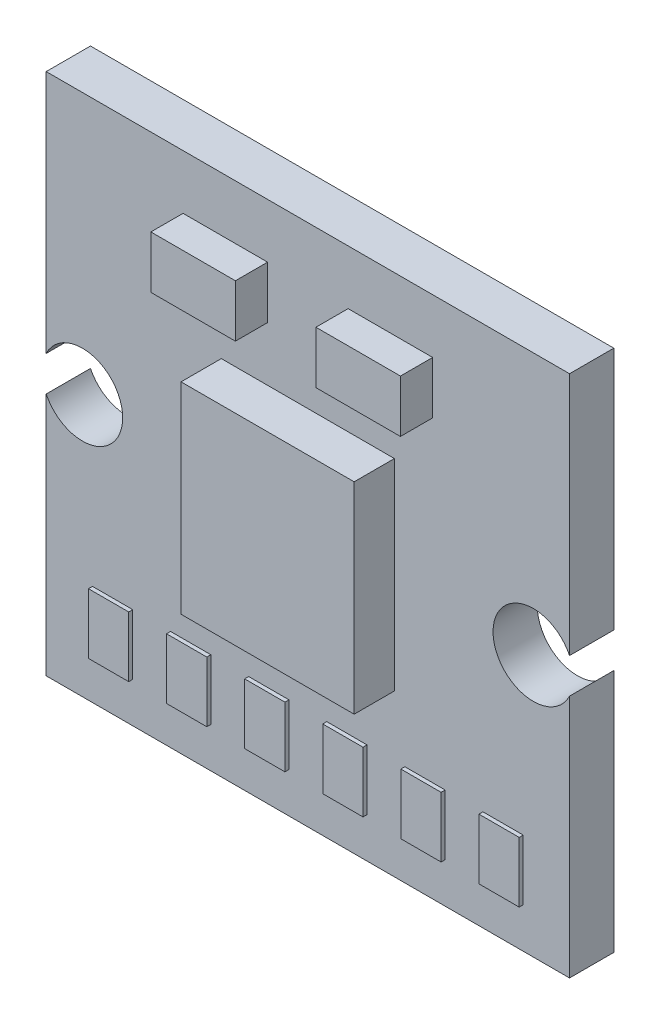
SolidWorks part; units mm, degrees
ref_plane "정면" through (0, 0, 0) normal (0, 0, 1) x (1, 0, 0)
ref_plane "윗면" through (0, 0, 0) normal (0, 1, 0) x (1, 0, 0)
ref_plane "우측면" through (0, 0, 0) normal (1, 0, 0) x (0, 0, -1)
sketch "스케치1" plane through (0, 0, 0) normal (0, 0, 1) x (1, 0, 0)
  line L1 (6.5, 6.5) -> (-6.5, 6.5)
  line L2 (6.5, 6.5) -> (6.5, -6.5)
  line L3 (6.5, -6.5) -> (-6.5, -6.5)
  line L4 (-6.5, 6.5) -> (-6.5, -6.5)
  point P0 (0, 6.5)
  point P1 (6.5, 0)
  dimension "D1" = 13
  dimension "D2" = 13
extrude "보스-돌출1" add sketch "스케치1" along normal blind 1.1
sketch "스케치2" plane through (0, 0, 1.1) normal (0, 0, 1) x (1, 0, 0)
  line L1 (-2.15, -2.5) -> (2.15, -2.5)
  line L2 (-2.15, -2.5) -> (-2.15, 2.5)
  line L3 (-2.15, 2.5) -> (2.15, 2.5)
  line L4 (2.15, -2.5) -> (2.15, 2.5)
  line L5 (-2.15, -2.5) -> (2.15, 2.5) construction
  line L6 (-2.15, 2.5) -> (2.15, -2.5) construction
  point P0 (0, 0)
  point P6 (0, 0)
  dimension "D1" = 5
  dimension "D2" = 4.3
extrude "보스-돌출2" add sketch "스케치2" along normal offset from surface (1 mm away) 2.1 up to face at (0, 0, 0)
sketch "스케치3" plane through (0, 0, 1.1) normal (0, 0, 1) x (1, 0, 0)
  line L0 (6.5, -6.5) -> (6.5, 6.5) construction
  line L1 (-3.1, 5.15) -> (-1, 5.15)
  line L2 (-3.1, 5.15) -> (-3.1, 3.85)
  line L3 (-3.1, 3.85) -> (-1, 3.85)
  line L4 (-1, 5.15) -> (-1, 3.85)
  line L5 (1, 5.15) -> (3.1, 5.15)
  line L6 (1, 5.15) -> (1, 3.85)
  line L7 (1, 3.85) -> (3.1, 3.85)
  line L8 (3.1, 5.15) -> (3.1, 3.85)
  line L9 (6.5, 6.5) -> (-6.5, 6.5) construction
  dimension "D1" = 1.35
  dimension "D2" = 1.3
  dimension "D3" = 2.1
  dimension "D4" = 2
  dimension "D5" = 3.4
extrude "보스-돌출3" add sketch "스케치3" along normal offset from surface (0.8 mm away) 1.9 up to face at (0, 0, 0)
sketch "스케치4" plane through (0, 0, 1.1) normal (0, 0, 1) x (1, 0, 0)
  line L0 (-6.5, 6.5) -> (-6.5, -6.5) construction
  line L1 (-6.5, -6.5) -> (6.5, -6.5) construction
  line L3 (-3.41, -4) -> (-2.41, -4)
  line L4 (-3.41, -4) -> (-3.41, -5.5)
  line L5 (-3.41, -5.5) -> (-2.41, -5.5)
  line L6 (5.35, -5.5) -> (4.35, -5.5)
  line L7 (5.35, -5.5) -> (5.35, -4)
  line L8 (5.35, -4) -> (4.35, -4)
  line L9 (4.35, -5.5) -> (4.35, -4)
  line L10 (-5.35, -4) -> (-4.35, -4)
  line L11 (-5.35, -4) -> (-5.35, -5.5)
  line L12 (-5.35, -5.5) -> (-4.35, -5.5)
  line L13 (-4.35, -4) -> (-4.35, -5.5)
  line L14 (-2.41, -4) -> (-2.41, -5.5)
  line L15 (-1.47, -4) -> (-0.47, -4)
  line L16 (-1.47, -4) -> (-1.47, -5.5)
  line L17 (-1.47, -5.5) -> (-0.47, -5.5)
  line L18 (-0.47, -4) -> (-0.47, -5.5)
  line L19 (0.47, -4) -> (1.47, -4)
  line L20 (0.47, -4) -> (0.47, -5.5)
  line L21 (0.47, -5.5) -> (1.47, -5.5)
  line L22 (1.47, -4) -> (1.47, -5.5)
  line L23 (2.41, -4) -> (3.41, -4)
  line L24 (2.41, -4) -> (2.41, -5.5)
  line L25 (2.41, -5.5) -> (3.41, -5.5)
  line L26 (3.41, -4) -> (3.41, -5.5)
  point P29 (-2.2779, -5.8729)
  dimension "D1" = 10.7
  dimension "D2" = 1.15
  dimension "D3" = 1
  dimension "D4" = 1.5
  dimension "D5" = 1
  dimension "D6" = 0.94
  dimension "D7" = 0.94
  dimension "D8" = 0.94
  dimension "D9" = 0.94
extrude "보스-돌출4" add sketch "스케치4" along normal blind 0.1
sketch "스케치5" plane through (0, 0, 1.1) normal (0, 0, 1) x (1, 0, 0)
  circle A0 centre (5.6, 0) radius 1
  circle A1 centre (-5.6, 0) radius 1
  point P4 (0, 0)
  dimension "D2" = 2
  dimension "D3" = 2
  dimension "D1" = 11.2
  dimension "D4" = 5.6
extrude "컷-돌출1" cut sketch "스케치5" against normal up to surface (1.1 mm away) up to face at (0, 0, 0)
